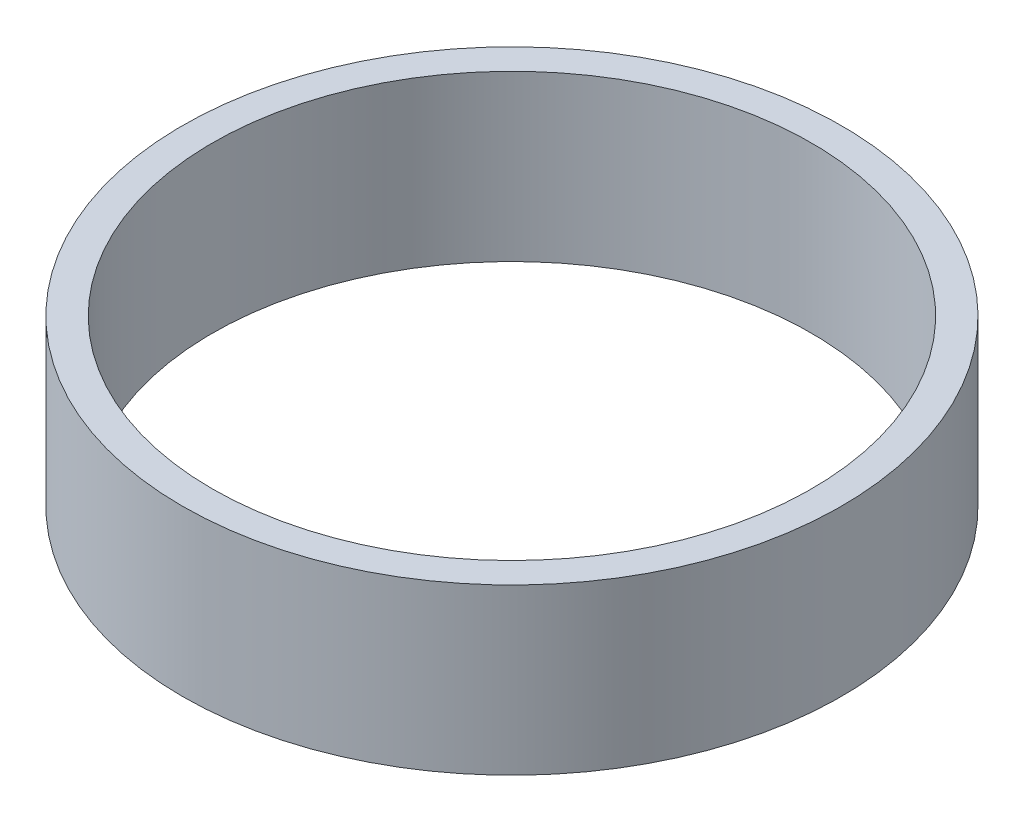
SolidWorks part; units mm, degrees
ref_plane "Front Plane" through (0, 0, 0) normal (0, 0, 1) x (1, 0, 0)
ref_plane "Top Plane" through (0, 0, 0) normal (0, 1, 0) x (1, 0, 0)
ref_plane "Right Plane" through (0, 0, 0) normal (1, 0, 0) x (0, 0, -1)
sketch "Sketch1" plane through (0, 0, 0) normal (0, 1, 0) x (1, 0, 0)
  circle A0 centre (0, 0) radius 44
  circle A1 centre (0, 0) radius 40
  dimension "D1" = 4
  dimension "D2" = 80
extrude "Boss-Extrude1" add sketch "Sketch1" along normal blind 22
